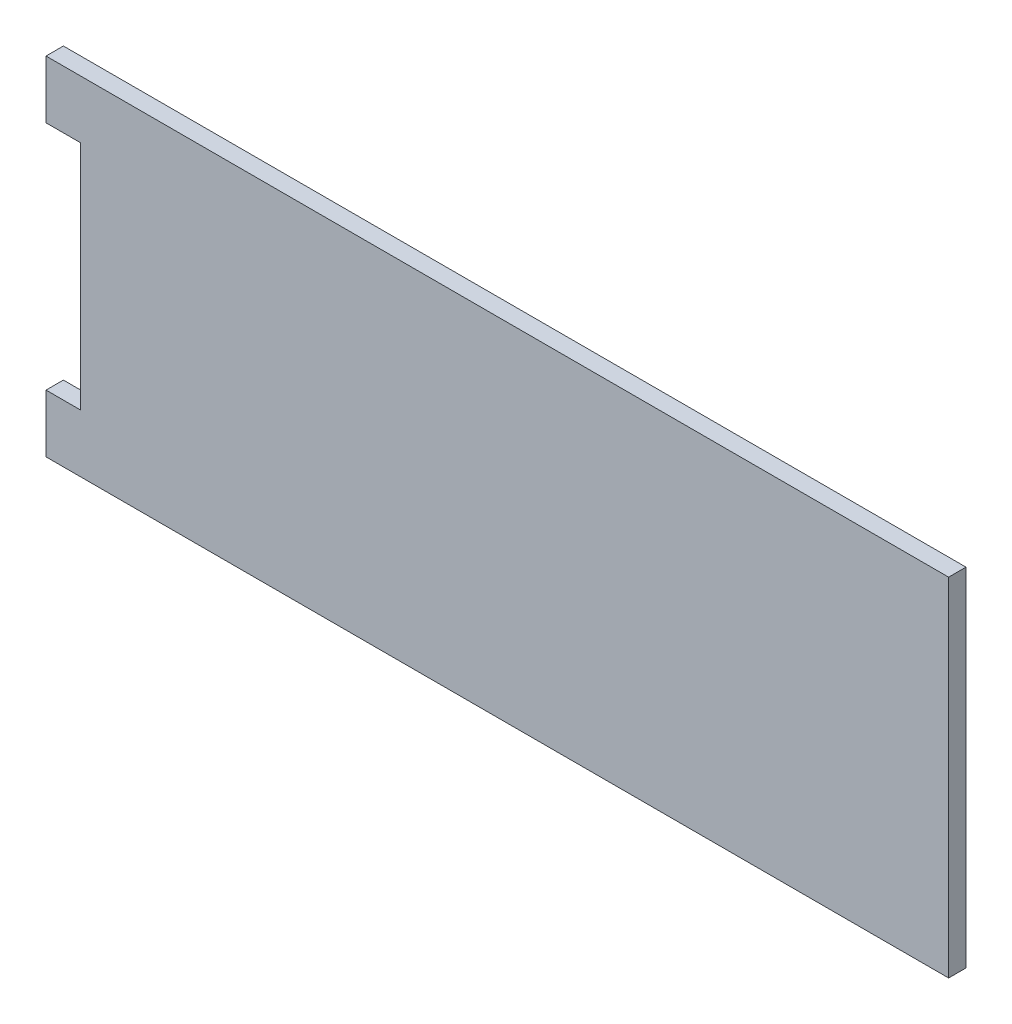
SolidWorks part; units mm, degrees
ref_plane "Plan de face" through (0, 0, 0) normal (0, 0, 1) x (1, 0, 0)
ref_plane "Plan de dessus" through (0, 0, 0) normal (0, 1, 0) x (1, 0, 0)
ref_plane "Plan de droite" through (0, 0, 0) normal (1, 0, 0) x (0, 0, -1)
sketch "Esquisse1" plane through (0, 0, 0) normal (0, 0, 1) x (1, 0, 0)
  line L1 (-111.5878, 105.9926) -> (38.4122, 105.9926)
  line L2 (-111.5878, 95.9926) -> (-111.5878, 55.9926)
  line L3 (-111.5878, 45.9926) -> (38.4122, 45.9926)
  line L4 (38.4122, 105.9926) -> (38.4122, 45.9926)
  line L5 (-111.5878, 105.9926) -> (-117.5878, 105.9926)
  line L7 (-111.5878, 95.9926) -> (-117.5878, 95.9926)
  line L8 (-117.5878, 105.9926) -> (-117.5878, 95.9926)
  line L9 (-111.5878, 55.9926) -> (-117.5878, 55.9926)
  line L11 (-111.5878, 45.9926) -> (-117.5878, 45.9926)
  line L12 (-117.5878, 55.9926) -> (-117.5878, 45.9926)
  point P0 (-109.7297, 45.9926)
  point P12 (-110.4874, 100.1742)
  dimension "D1" = 150
  dimension "D2" = 60
  dimension "D3" = 6
  dimension "D4" = 10
  dimension "D5" = 6
  dimension "D6" = 10
extrude "Boss.-Extru.1" add sketch "Esquisse1" along normal blind 3
